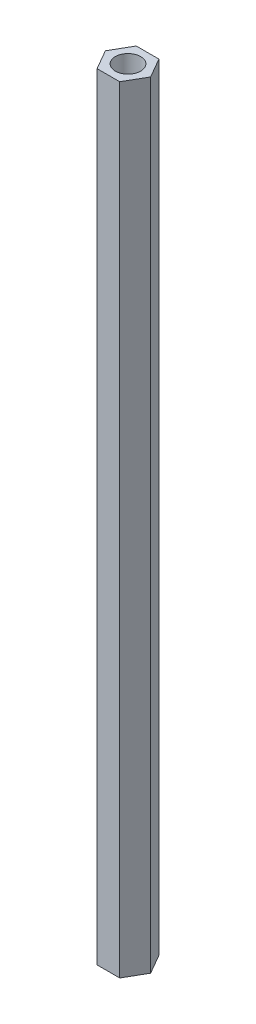
SolidWorks part; units mm, degrees
ref_plane "Front Plane" through (0, 0, 0) normal (0, 0, 1) x (1, 0, 0)
ref_plane "Top Plane" through (0, 0, 0) normal (0, 1, 0) x (1, 0, 0)
ref_plane "Right Plane" through (0, 0, 0) normal (1, 0, 0) x (0, 0, -1)
sketch "Sketch1" plane through (0, 0, 0) normal (0, 1, 0) x (1, 0, 0)
  line L0 (1.3414, 2.3233) -> (2.6828, 0)
  line L1 (-1.3414, 2.3233) -> (1.3414, 2.3233)
  line L2 (2.6828, 0) -> (1.3414, -2.3233)
  line L3 (1.3414, -2.3233) -> (-1.3414, -2.3233)
  line L4 (-1.3414, -2.3233) -> (-2.6828, 0)
  line L5 (-2.6828, 0) -> (-1.3414, 2.3233)
  circle A0 centre (0, 0) radius 1.5
  dimension "D1" = 3
  dimension "D3" = 6
extrude "Boss-Extrude1" add sketch "Sketch1" along normal blind 92
